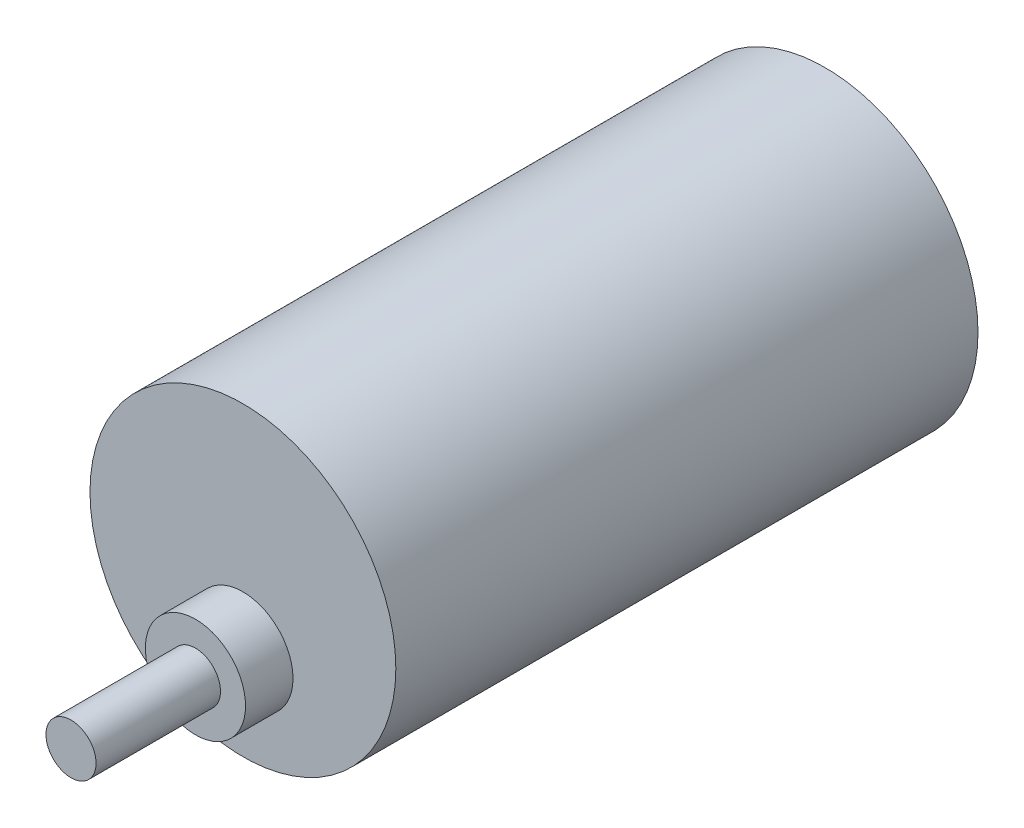
SolidWorks part; units mm, degrees
ref_plane "Front Plane" through (0, 0, 0) normal (0, 0, 1) x (1, 0, 0)
ref_plane "Top Plane" through (0, 0, 0) normal (0, 1, 0) x (1, 0, 0)
ref_plane "Right Plane" through (0, 0, 0) normal (1, 0, 0) x (0, 0, -1)
sketch "Sketch2" plane through (0, 0, 0) normal (0, 0, 1) x (1, 0, 0)
  circle A0 centre (0, 0) radius 18.415
  dimension "D1" = 36.83
extrude "Boss-Extrude1" add sketch "Sketch2" along normal blind 70.104
sketch "Sketch3" plane through (0, 0, 70.104) normal (0, 0, 1) x (1, 0, 0)
  line L0 (0, 0) -> (0, -18.415) construction
  circle A0 centre (0, 0) radius 18.415 construction
  circle A1 centre (0, -7.239) radius 6.0325
  dimension "D1" = 11.176
  dimension "D2" = 12.065
extrude "Boss-Extrude2" add sketch "Sketch3" along normal blind 5.715
sketch "Sketch5" plane through (0, 0, 75.819) normal (0, 0, 1) x (1, 0, 0)
  circle A0 centre (0, -7.239) radius 3.0162
  dimension "D1" = 6.0325
extrude "Boss-Extrude3" add sketch "Sketch5" along normal blind 14.986
